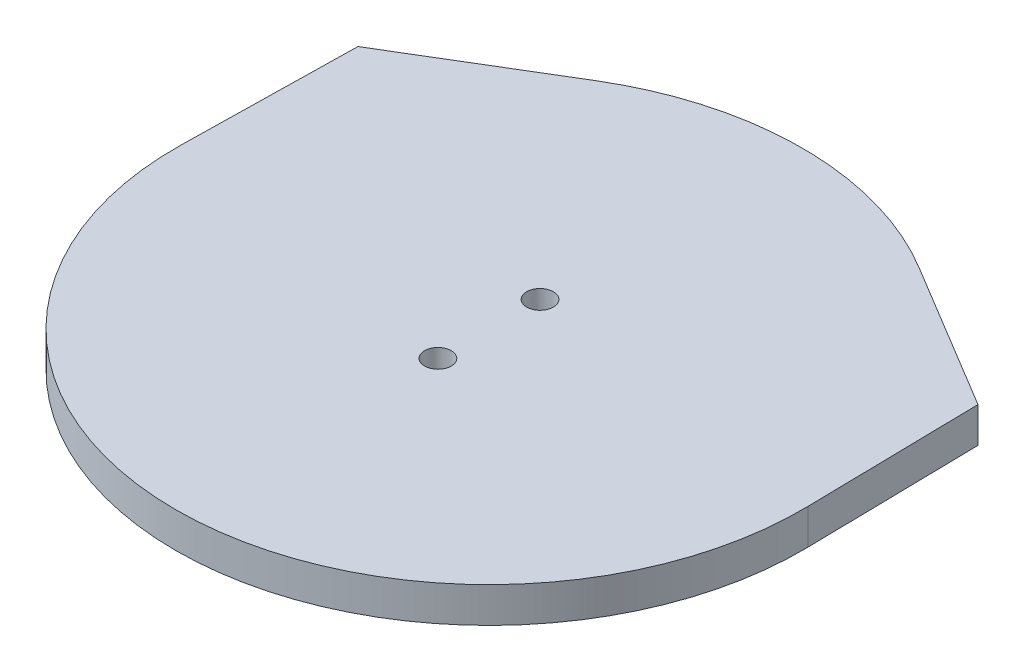
SolidWorks part; units mm, degrees
ref_plane "Front Plane" through (0, 0, 0) normal (0, 0, 1) x (1, 0, 0)
ref_plane "Top Plane" through (0, 0, 0) normal (0, 1, 0) x (1, 0, 0)
ref_plane "Right Plane" through (0, 0, 0) normal (1, 0, 0) x (0, 0, -1)
sketch "Sketch6" plane through (0, 0, 0) normal (0, 1, 0) x (1, 0, 0)
  line L8 (-37.735, 17.5894) -> (-18.833, 28.9671)
  line L9 (41.197, 17.5894) -> (22.295, 28.9671)
  line L10 (41.197, 17.5894) -> (41.5994, -4.4691)
  line L11 (-38.1374, -4.4691) -> (-37.735, 17.5894)
  arc A4 (22.295, 28.9671) -> (-18.833, 28.9671) centre (1.731, -5.1963) ccw
  circle A5 centre (1.731, 94.8037) radius 25 construction
  arc A6 (-38.1374, -4.4691) -> (41.5994, -4.4691) centre (1.731, -5.1963) ccw
  point P39 (-42.5504, 25.0018)
  point P40 (23.25, 50)
  point P41 (0, 50)
  point P42 (-20.8013, 25)
  point P43 (-20.0513, 25)
  point P45 (-43.3013, 25)
  point P46 (22.5, 50)
  point P51 (0, 50)
extrude "Boss-Extrude4" add sketch "Sketch6" along normal blind 4.5 separate body
sketch "Sketch8" plane through (0, 0, 0) normal (0, 1, 0) x (1, 0, 0)
  line L0 (1.731, 94.8037) -> (1.731, -25.8418) construction
  line L2 (1.731, -5.1963) -> (73.5507, -5.1963) construction
  circle A0 centre (1.731, 94.8037) radius 25 construction
  circle A1 centre (1.731, -5.1963) radius 12.7 construction
  circle A2 centre (1.731, -5.1963) radius 6.5 construction
  dimension "D1" = 13
hole_wizard "CSK for M3 Flat Head Machine Screw1" positions "Sketch14" profile "Sketch13" countersink size "M3" standard "ANSI Metric" end condition through all
sketch "Sketch14" plane through (0, 0, 5.6) normal (0, -1, 0) x (1, 0, 0)
  line L0 (1.731, -100.4037) -> (1.731, 20.2418) construction
  circle A0 centre (1.731, -0.4037) radius 6.5 construction
  point P0 (1.731, -6.9037)
  point P6 (1.731, 6.0963)
sketch "Sketch13" plane through (1.731, 0, -1.3037) normal (1, 0, 0) x (0, 0, -1)
  line L0 (0, 0) -> (0, 4.5)
  line L1 (0, 4.5) -> (1.7, 4.5)
  line L2 (1.7, 4.5) -> (1.7, 1.45)
  line L3 (1.7, 1.45) -> (3.15, 0)
  line L5 (3.15, 0) -> (0, 0)
  line L6 (-1.7, 1.45) -> (-3.15, 0) construction
  line L11 (0, -6.35) -> (0, 107.95) construction
  dimension "Thru Hole Dia." = 3.4
  dimension "Thru Hole Depth" = 4.5
  dimension "Near C'Sink Dia." = 6.3
  dimension "Near C'Sink Angle" = 90
